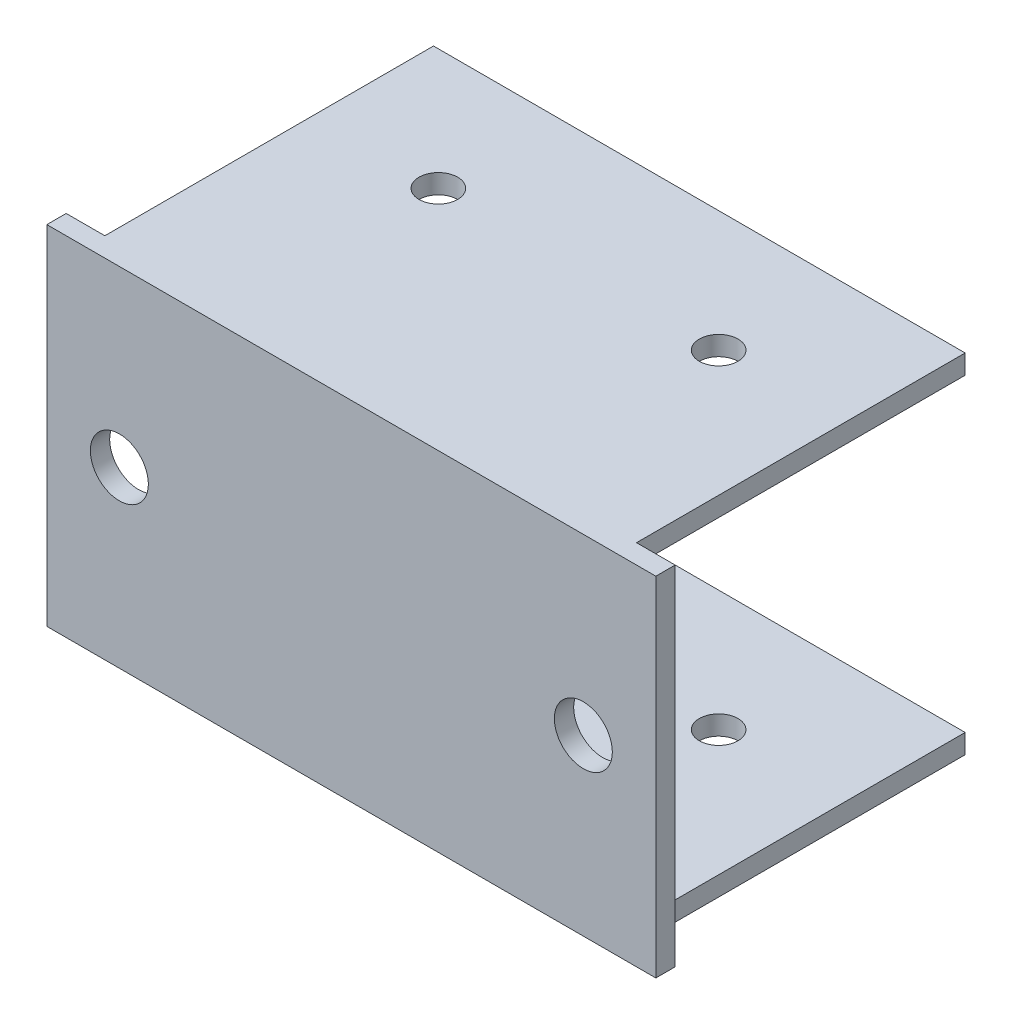
SolidWorks part; units mm, degrees
ref_plane "前视基准面" through (0, 0, 0) normal (0, 0, 1) x (1, 0, 0)
ref_plane "上视基准面" through (0, 0, 0) normal (0, 1, 0) x (1, 0, 0)
ref_plane "右视基准面" through (0, 0, 0) normal (1, 0, 0) x (0, 0, -1)
sketch "草图1" plane through (0, 0, 0) normal (0, 0, 1) x (1, 0, 0)
  line L1 (-31.5, 18) -> (31.5, 18)
  line L2 (-31.5, 18) -> (-31.5, -18)
  line L3 (-31.5, -18) -> (31.5, -18)
  line L4 (31.5, 18) -> (31.5, -18)
  line L5 (-31.5, 18) -> (31.5, -18) construction
  line L6 (-31.5, -18) -> (31.5, 18) construction
  point P0 (0, 0)
  dimension "D1" = 63
  dimension "D2" = 36
extrude "凸台-拉伸1" add sketch "草图1" along normal blind 2 contours L2 L3 L4 L1
sketch "草图2" plane through (0, 0, 2) normal (0, 0, 1) x (1, 0, 0)
  line L0 (-24, 0) -> (24, 0) construction
  circle A0 centre (-24, 0) radius 3
  circle A1 centre (24, 0) radius 3
  point P2 (0, 0)
  dimension "D2" = 6
  dimension "D3" = 6
  dimension "D1" = 48
extrude "切除-拉伸1" cut sketch "草图2" against normal blind 10
sketch "草图4" plane through (0, 18, 0) normal (0, 1, 0) x (1, 0, 0)
  line L0 (-31.5, -2) -> (31.5, -2) construction
  line L1 (-27.5, 34) -> (27.5, 34)
  line L2 (-27.5, 34) -> (-27.5, -2)
  line L3 (-27.5, -2) -> (27.5, -2)
  line L4 (27.5, 34) -> (27.5, -2)
  line L5 (-27.5, 34) -> (27.5, -2) construction
  line L6 (-27.5, -2) -> (27.5, 34) construction
  point P0 (0, 16)
  dimension "D1" = 36
  dimension "D2" = 55
extrude "凸台-拉伸2" add sketch "草图4" against normal blind 2
sketch "草图5" plane through (0, 18, 0) normal (0, 1, 0) x (1, 0, 0)
  line L0 (-14.5, 21.5) -> (14.5, 21.5) construction
  line L1 (27.5, 34) -> (-27.5, 34) construction
  circle A0 centre (-14.5, 21.5) radius 2
  circle A1 centre (14.5, 21.5) radius 2
  point P2 (0, 21.5)
  dimension "D3" = 4
  dimension "D4" = 4
  dimension "D1" = 12.5
  dimension "D2" = 29
extrude "切除-拉伸2" cut sketch "草图5" against normal through all
mirror "镜向1" about plane through (0, 0, 0) normal (0, 1, 0) of "切除-拉伸2", "凸台-拉伸2"
